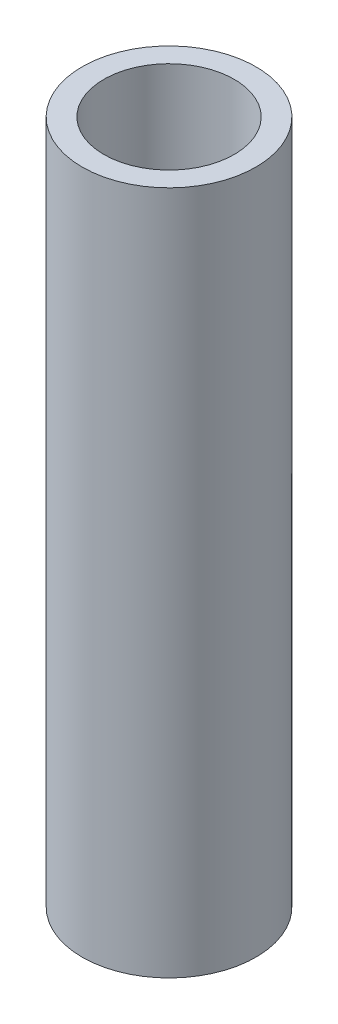
SolidWorks part; units mm, degrees
material "6061-T6 (SS)"
ref_plane "Front Plane" through (0, 0, 0) normal (0, 0, 1) x (1, 0, 0)
ref_plane "Top Plane" through (0, 0, 0) normal (0, 1, 0) x (1, 0, 0)
ref_plane "Right Plane" through (0, 0, 0) normal (1, 0, 0) x (0, 0, -1)
sketch "Sketch1" plane through (0, 0, 0) normal (0, 1, 0) x (1, 0, 0)
  circle A0 centre (0, 0) radius 25.4
  circle A1 centre (0, 0) radius 19.05
  dimension "D1" = 50.8
  dimension "D2" = 38.1
extrude "Boss-Extrude1" add sketch "Sketch1" along normal blind 200
